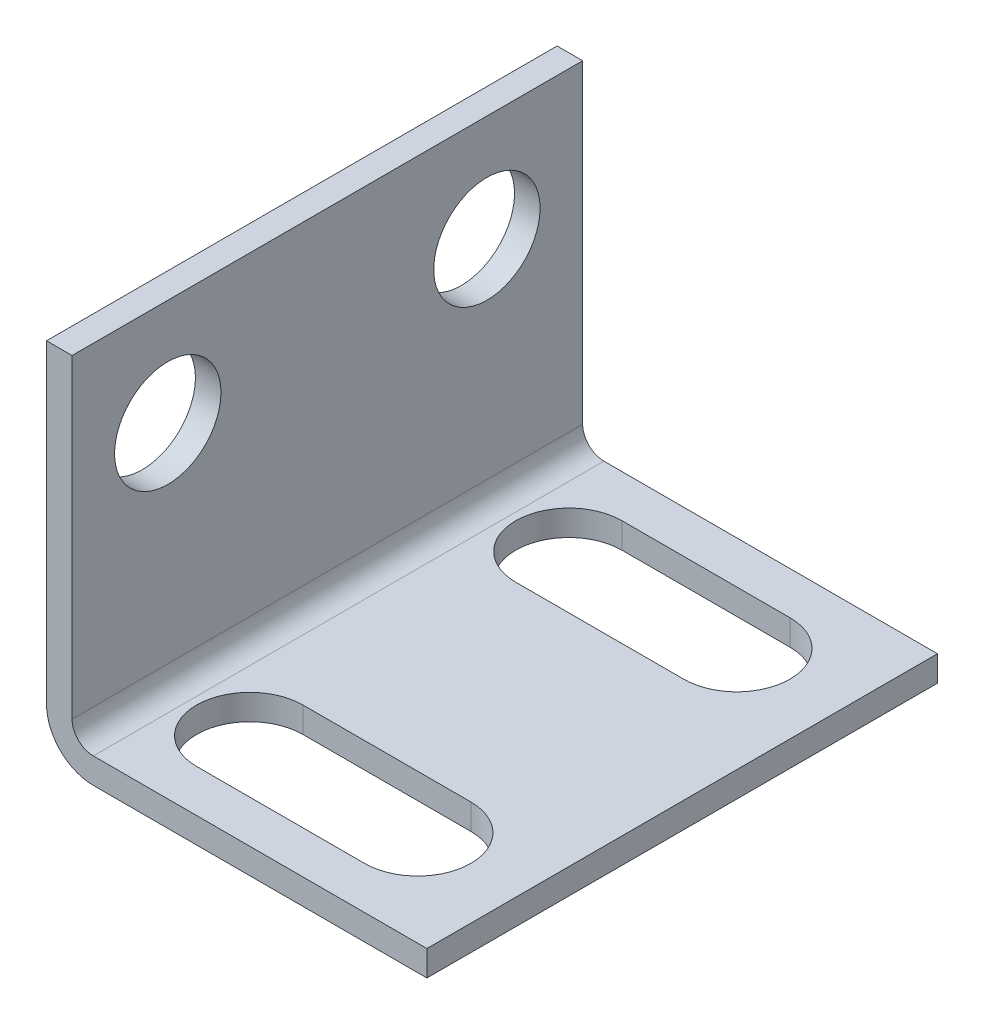
SolidWorks part; units mm, degrees
ref_plane "Front" through (0, 0, 0) normal (0, 0, 1) x (1, 0, 0)
ref_plane "Top" through (0, 0, 0) normal (0, 1, 0) x (1, 0, 0)
ref_plane "Right" through (0, 0, 0) normal (1, 0, 0) x (0, 0, -1)
sketch "Sketch1" plane through (0, 0, 0) normal (1, 0, 0) x (0, 0, -1)
  line L0 (0, 0) -> (0, 17)
  line L1 (0, 17) -> (24, 17)
  line L2 (24, 17) -> (24, 0)
  line L3 (24, 0) -> (0, 0)
  circle A0 centre (4.5, 12) radius 2.5
  circle A1 centre (19.5, 12) radius 2.5
  dimension "D1" = 5
  dimension "D2" = 17
  dimension "D3" = 12
  dimension "D4" = 15
  dimension "D5" = 24
  dimension "D6" = 4.5
sketch "Sketch3" plane through (0, 0, 0) normal (0, 1, 0) x (1, 0, 0)
  line L0 (0, 24) -> (0, 0)
  line L1 (0, 24) -> (0, 0) construction
  line L2 (0, 0) -> (17.88, 0)
  line L3 (17.88, 0) -> (17.88, 24)
  line L4 (17.88, 24) -> (0, 24)
  line L5 (5.0528, 19.5) -> (12.9472, 19.5) construction
  line L6 (5.0528, 22) -> (12.9472, 22)
  line L7 (5.0528, 17) -> (12.9472, 17)
  line L8 (5.0528, 4.5) -> (12.9472, 4.5) construction
  line L9 (5.0528, 7) -> (12.9472, 7)
  line L10 (5.0528, 2) -> (12.9472, 2)
  arc A0 (5.0528, 22) -> (5.0528, 17) centre (5.0528, 19.5) ccw
  arc A1 (12.9472, 17) -> (12.9472, 22) centre (12.9472, 19.5) ccw
  arc A2 (5.0528, 7) -> (5.0528, 2) centre (5.0528, 4.5) ccw
  arc A3 (12.9472, 2) -> (12.9472, 7) centre (12.9472, 4.5) ccw
  point P9 (9, 19.5)
  point P14 (9, 4.5)
  dimension "D7" = 2.5
  dimension "D8" = 2.5
  dimension "D1" = 17.88
  dimension "D2" = 4.5
  dimension "D3" = 15
  dimension "D4" = 24
  dimension "D5" = 9
  dimension "D6" = 9
extrude "Boss-Extrude1" add sketch "Sketch1" along normal blind 1.2
extrude "Boss-Extrude3" add sketch "Sketch3" along normal blind 1.2
fillet "Fillet1" radius 1 1 edges at (1.2, 1.2, -12)
fillet "Fillet2" radius 2.2 1 edges at (0, 0, -12)
